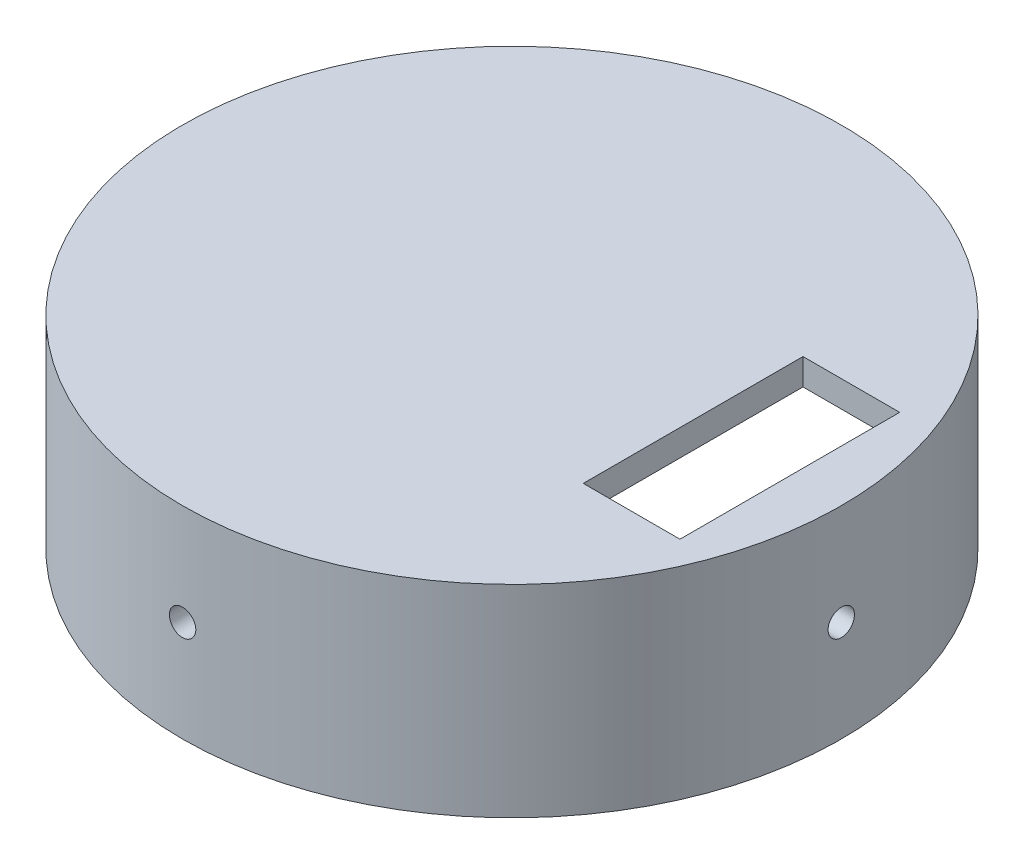
SolidWorks part; units mm, degrees
ref_plane "Front Plane" through (0, 0, 0) normal (0, 0, 1) x (1, 0, 0)
ref_plane "Top Plane" through (0, 0, 0) normal (0, 1, 0) x (1, 0, 0)
ref_plane "Right Plane" through (0, 0, 0) normal (1, 0, 0) x (0, 0, -1)
sketch "Sketch1" plane through (0, 0, 0) normal (0, 1, 0) x (1, 0, 0)
  circle A0 centre (0, 0) radius 37.5
  circle A1 centre (0, 0) radius 34
  dimension "D1" = 75
  dimension "D2" = 3.5
extrude "Boss-Extrude1" add sketch "Sketch1" along normal blind 20
sketch "Sketch2" plane through (0, 20, 0) normal (0, 1, 0) x (1, 0, 0)
  circle A0 centre (0, 0) radius 37.5
  dimension "D1" = 75
extrude "Boss-Extrude2" add sketch "Sketch2" along normal blind 3 contours A0
sketch "Sketch3" plane through (0, 23, 0) normal (0, 1, 0) x (1, 0, 0)
  line L0 (0, 0) -> (37.5, 0) construction
  line L6 (20.6188, -12.5) -> (31.6188, -12.5)
  line L7 (20.6188, -12.5) -> (20.6188, 12.5)
  line L8 (20.6188, 12.5) -> (31.6188, 12.5)
  line L9 (31.6188, -12.5) -> (31.6188, 12.5)
  line L10 (20.6188, -12.5) -> (31.6188, 12.5) construction
  line L11 (20.6188, 12.5) -> (31.6188, -12.5) construction
  circle A0 centre (0, 0) radius 37.5 construction
  circle A1 centre (0, 0) radius 34 construction
  point P0 (26.1188, 0)
  point P10 (22.5845, 0)
  point P11 (0, 0)
  point P12 (23.2035, 0)
  point P13 (0, 0)
  point P14 (0, 0)
  point P15 (23.7194, 0)
  point P16 (0, 0)
  point P17 (31.6632, 12.3872)
  point P20 (31.6188, 12.5)
  point P21 (31.6188, 12.5)
  point P22 (31.6188, 12.5)
  dimension "D1" = 11
  dimension "D2" = 25
extrude "Cut-Extrude1" cut sketch "Sketch3" against normal blind 3
sketch "Sketch4" plane through (0, 0, 0) normal (0, 0, 1) x (1, 0, 0)
  line L0 (0, 23) -> (0, 0) construction
  line L1 (37.5, 23) -> (-37.5, 23) construction
  circle A1 centre (0, 11.5) radius 1.5
  dimension "D1" = 3
extrude "Cut-Extrude2" cut sketch "Sketch4" against normal blind 80 and the other way blind 80
sketch "Sketch5" plane through (0, 0, 0) normal (1, 0, 0) x (0, 0, -1)
  line L0 (0, 0) -> (0, 23) construction
  line L1 (-12.5, 23) -> (12.5, 23) construction
  circle A0 centre (0, 11.5) radius 1.5
  dimension "D1" = 3
extrude "Cut-Extrude4" cut sketch "Sketch5" against normal blind 80 and the other way blind 80 contours A0
